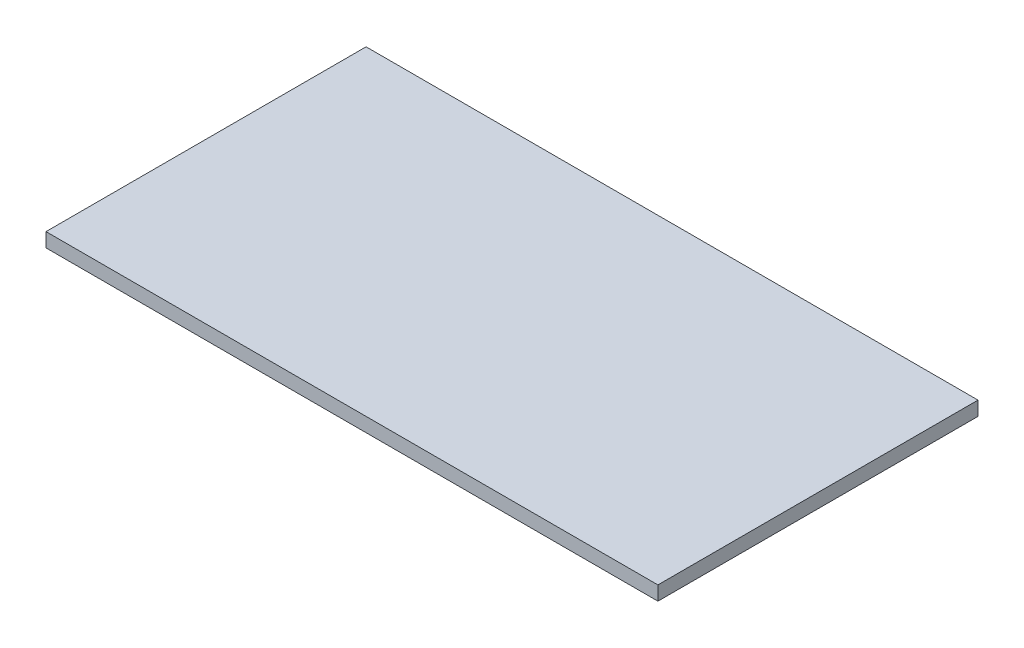
SolidWorks part; units mm, degrees
ref_plane "Front Plane" through (0, 0, 0) normal (0, 0, 1) x (1, 0, 0)
ref_plane "Top Plane" through (0, 0, 0) normal (0, 1, 0) x (1, 0, 0)
ref_plane "Right Plane" through (0, 0, 0) normal (1, 0, 0) x (0, 0, -1)
sketch "Sketch1" plane through (0, 0, 0) normal (0, 1, 0) x (1, 0, 0)
  line L1 (-16.3868, -18.6227) -> (113.6132, -18.6227)
  line L2 (-16.3868, -18.6227) -> (-16.3868, 49.3773)
  line L3 (-16.3868, 49.3773) -> (113.6132, 49.3773)
  line L4 (113.6132, -18.6227) -> (113.6132, 49.3773)
  dimension "D1" = 68
  dimension "D2" = 130
extrude "Boss-Extrude1" add sketch "Sketch1" along normal blind 3
